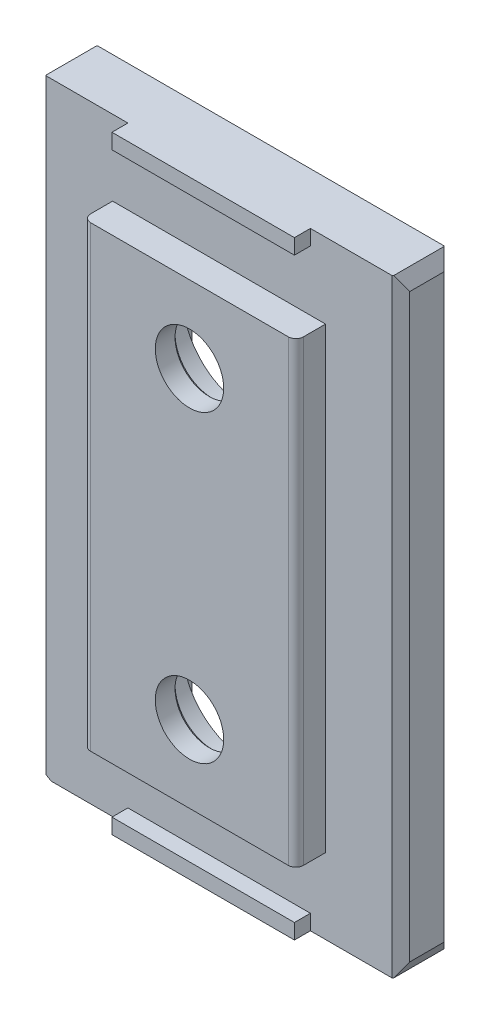
SolidWorks part; units mm, degrees
ref_plane "Front Plane" through (0, 0, 0) normal (0, 0, 1) x (1, 0, 0)
ref_plane "Top Plane" through (0, 0, 0) normal (0, 1, 0) x (1, 0, 0)
ref_plane "Right Plane" through (0, 0, 0) normal (1, 0, 0) x (0, 0, -1)
ref_plane "Plane1" through (0, 0, 7.55) normal (0, 0, 1) x (1, 0, 0)
sketch "Sketch1" plane through (0, 0, 7.55) normal (0, 0, 1) x (1, 0, 0)
  line L0 (-11.95, -20) -> (11.95, -20)
  line L1 (11.95, -20) -> (11.95, 20)
  line L2 (11.95, 20) -> (-11.95, 20)
  line L3 (-11.95, 20) -> (-11.95, -20)
extrude "Boss-Extrude1" add sketch "Sketch1" against normal blind 3.4
ref_plane "Plane2" through (0, -15, 0) normal (0, -1, 0) x (1, 0, 0)
sketch "Sketch2" plane through (0, -15, 0) normal (0, -1, 0) x (1, 0, 0)
  line L0 (7, 7.3107) -> (7, 7.55)
  line L1 (7, 7.55) -> (6.995, 7.55)
  line L2 (6.995, 7.55) -> (6.995, 7.4)
  arc A0 (6.995, 7.4) -> (7, 7.3107) centre (7.795, 7.4) ccw
extrude "Cut-Extrude1" cut sketch "Sketch2" against normal blind 30
sketch "Sketch3" plane through (0, 0, 7.55) normal (0, 0, 1) x (1, 0, 0)
  line L0 (6.995, -15.05) -> (-7.005, -15.05)
  line L1 (-7.005, -15.05) -> (-7.005, 15.05)
  line L2 (-7.005, 15.05) -> (6.995, 15.05)
  line L3 (6.995, 15.05) -> (6.995, -15.05)
extrude "Boss-Extrude2" add sketch "Sketch3" along normal blind 1.95
sketch "Sketch4" plane through (0, 0, 4.15) normal (0, 0, -1) x (-1, 0, 0)
  line L0 (-5.2, -15) -> (5.2, -15)
  line L1 (5.2, -15) -> (5.2, 15)
  line L2 (5.2, 15) -> (-5.2, 15)
  line L3 (-5.2, 15) -> (-5.2, -15)
extrude "Cut-Extrude2" cut sketch "Sketch4" against normal blind 1.55
ref_plane "Plane3" through (0, 0, 4.15) normal (0, 0, -1) x (-1, 0, 0)
ref_plane "Plane4" through (0, 0, 5.1) normal (0, 0, 1) x (1, 0, 0)
sketch "Sketch6" plane through (0, 0, 5.1) normal (0, 0, 1) x (1, 0, 0)
  line L0 (5.2, -16.75) -> (5.2, -15)
  line L1 (5.2, -15) -> (-5.2, -15)
  line L2 (-5.2, -15) -> (-5.2, -16.75)
  line L3 (-5.2, -16.75) -> (5.2, -16.75)
extrude "Cut-Extrude3" cut sketch "Sketch6" against normal up to surface up to plane "Plane3"
sketch "Sketch8" plane through (0, 0, 5.1) normal (0, 0, 1) x (1, 0, 0)
  line L0 (-5.2, 16.75) -> (-5.2, 15)
  line L1 (-5.2, 15) -> (5.2, 15)
  line L2 (5.2, 15) -> (5.2, 16.75)
  line L3 (5.2, 16.75) -> (-5.2, 16.75)
extrude "Cut-Extrude4" cut sketch "Sketch8" against normal up to surface up to plane "Plane3"
sketch "Sketch9" plane through (-5.2, 0, 0) normal (1, 0, 0) x (0, 0, -1)
  line L0 (-5.1, -15) -> (-5.1, 15)
  line L1 (-5.1, 15) -> (-5.7, 15)
  line L2 (-5.7, 15) -> (-5.7, -15)
  line L3 (-5.7, -15) -> (-5.1, -15)
extrude "Cut-Extrude5" cut sketch "Sketch9" against normal blind 1.8
sketch "Sketch10" plane through (5.2, 0, 0) normal (-1, 0, 0) x (0, 0, 1)
  line L0 (5.1, 15) -> (5.1, -15)
  line L1 (5.1, -15) -> (5.7, -15)
  line L2 (5.7, -15) -> (5.7, 15)
  line L3 (5.7, 15) -> (5.1, 15)
extrude "Cut-Extrude6" cut sketch "Sketch10" against normal blind 1.8
sketch "Sketch11" plane through (0, 0, 7.55) normal (0, 0, 1) x (1, 0, 0)
  line L0 (6, 20) -> (6, 19)
  line L1 (6, 19) -> (-6, 19)
  line L2 (-6, 19) -> (-6, 20)
  line L3 (-6, 20) -> (6, 20)
extrude "Boss-Extrude3" add sketch "Sketch11" along normal blind 1.05
sketch "Sketch12" plane through (0, 0, 7.55) normal (0, 0, 1) x (1, 0, 0)
  line L0 (6, -19) -> (6, -20)
  line L1 (6, -20) -> (-6, -20)
  line L2 (-6, -20) -> (-6, -19)
  line L3 (-6, -19) -> (6, -19)
extrude "Boss-Extrude4" add sketch "Sketch12" along normal blind 1.05
hole_wizard "CBORE for M4 Hex Head Machine Screw1" positions "Sketch14" profile "Sketch13" counterbore size "M4" standard "ANSI Metric"
sketch "Sketch14" plane through (0, 0, 5.7) normal (0, 0, -1) x (-1, 0, 0)
  point P0 (0, 10)
  point P1 (0, -10)
sketch "Sketch13" plane through (0, 10, 5.7) normal (1, 0, 0) x (0, 1, 0)
  line L0 (0, 0) -> (0, 3.8)
  line L1 (0, 3.8) -> (2.25, 3.8)
  line L3 (2.25, 3.8) -> (2.25, 2.3)
  line L4 (2.25, 2.3) -> (4.25, 2.3)
  line L5 (4.25, 2.3) -> (4.25, 0)
  line L7 (4.25, 0) -> (0, 0)
  line L11 (0, -6.35) -> (0, 107.95) construction
  dimension "Thru Hole Dia." = 4.5
  dimension "Thru Hole Depth" = 3.8
  dimension "C'Bore Dia." = 8.5
  dimension "C'Bore Depth" = 2.3
chamfer "Chamfer1" distance 0.527 angle 60.015 3 edges at (-11.95, -20, 5.85) (-11.95, 20, 5.85) (11.95, -20, 5.85)
chamfer "Chamfer2" distance 0.2 angle 45 2 edges at (-2.25, -10, 8) (-2.25, 10, 8)
chamfer "Chamfer3" distance 0.577 angle 45 4 edges at (11.95, 0.4567, 7.55) (11.95, 0.4567, 4.15) (-11.95, -0.1932, 4.15) (-11.95, -0.1932, 7.55)
chamfer "Chamfer4" distance 0.9133 angle 29.985 1 edges at (11.95, 20, 5.85)
fillet "Fillet1" radius 0.5 2 edges at (6.995, 0, 9.5) (-7.005, 0, 9.5)
